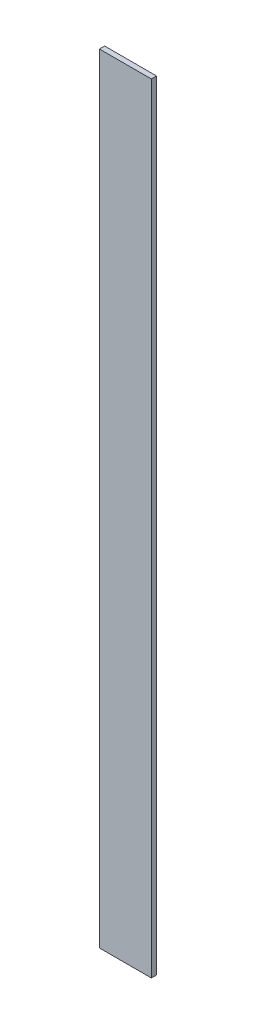
SolidWorks part; units mm, degrees
ref_plane "Plano frontal" through (0, 0, 0) normal (0, 0, 1) x (1, 0, 0)
ref_plane "Plano superior" through (0, 0, 0) normal (0, 1, 0) x (1, 0, 0)
ref_plane "Plano direito" through (0, 0, 0) normal (1, 0, 0) x (0, 0, -1)
sketch "Esboço1" plane through (0, 0, 0) normal (0, 1, 0) x (1, 0, 0)
  line L5 (-1156.4837, 804.6872) -> (-956.4837, 804.6872)
  line L6 (-1156.4837, 804.6872) -> (-1156.4837, 784.6872)
  line L7 (-1156.4837, 784.6872) -> (-956.4837, 784.6872)
  line L8 (-956.4837, 804.6872) -> (-956.4837, 784.6872)
  dimension "D1" = 200
  dimension "D2" = 20
extrude "Ressalto-extrusão1" add sketch "Esboço1" along normal blind 3000 contours L5 L8 L7 L6
